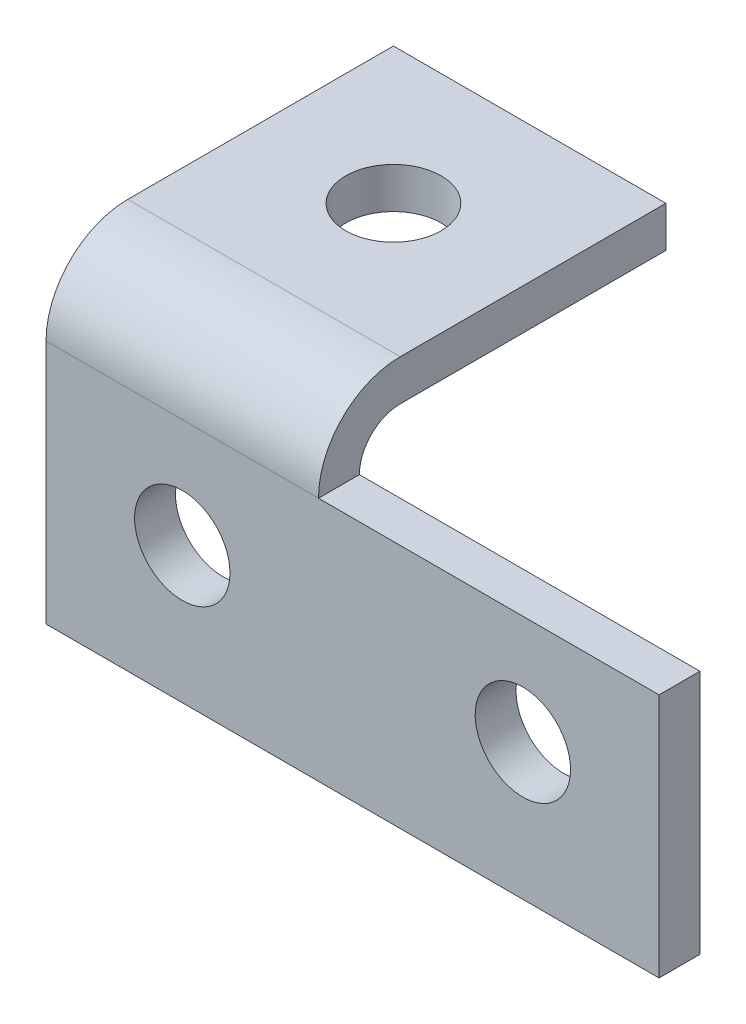
SolidWorks part; units mm, degrees
ref_plane "Front Plane" through (0, 0, 0) normal (0, 0, 1) x (1, 0, 0)
ref_plane "Top Plane" through (0, 0, 0) normal (0, 1, 0) x (1, 0, 0)
ref_plane "Right Plane" through (0, 0, 0) normal (1, 0, 0) x (0, 0, -1)
ref_plane "Plane1" through (-50, 0, 0) normal (1, 0, 0) x (0, 0, -1)
sketch "Sketch1" plane through (-50, 0, 0) normal (1, 0, 0) x (0, 0, -1)
  line L0 (0, 0) -> (51, 0)
  line L1 (51, 0) -> (51, 48)
  line L2 (51, 48) -> (12, 48)
  line L3 (0, 36) -> (0, 0)
  arc A0 (12, 48) -> (0, 36) centre (12, 36) ccw
extrude "Boss-Extrude1" add sketch "Sketch1" against normal blind 40
sketch "Sketch2" plane through (-90, 0, 0) normal (-1, 0, 0) x (0, 0, 1)
  line L0 (-51, 0) -> (-6, 0)
  line L1 (-6, 0) -> (-6, 36)
  line L2 (-12, 42) -> (-51, 42)
  line L3 (-51, 42) -> (-51, 0)
  arc A0 (-6, 36) -> (-12, 42) centre (-12, 36) ccw
extrude "Cut-Extrude1" cut sketch "Sketch2" against normal through all
sketch "Sketch3" plane through (-50, 0, 0) normal (1, 0, 0) x (0, 0, -1)
  line L0 (6, 0) -> (0, 0)
  line L1 (0, 0) -> (0, 36)
  line L2 (0, 36) -> (6, 36)
  line L3 (6, 36) -> (6, 0)
extrude "Boss-Extrude2" add sketch "Sketch3" along normal blind 50
hole_wizard "Ø14.0 (14) Diameter Hole1" positions "Sketch5" profile "Sketch4" hole size "Ø14.0" standard "ANSI Metric"
sketch "Sketch5" plane through (0, 0, 0) normal (0, 0, 1) x (1, 0, 0)
  point P0 (-70, 20)
sketch "Sketch4" plane through (-70, 20, 0) normal (1, 0, 0) x (0, -1, 0)
  line L0 (0, 0) -> (0, 51)
  line L1 (0, 51) -> (7, 51)
  line L2 (7, 51) -> (7, 0)
  line L5 (7, 0) -> (0, 0)
  line L11 (0, -6.35) -> (0, 107.95) construction
  dimension "Thru Hole Dia." = 14
  dimension "Thru Hole Depth" = 51
hole_wizard "Ø14.0 (14) Diameter Hole2" positions "Sketch7" profile "Sketch6" hole size "Ø14.0" standard "ANSI Metric"
sketch "Sketch7" plane through (0, 0, -6) normal (0, 0, -1) x (-1, 0, 0)
  point P0 (20, 20)
sketch "Sketch6" plane through (-20, 20, -6) normal (1, 0, 0) x (0, 1, 0)
  line L0 (0, 0) -> (0, 6)
  line L1 (0, 6) -> (7, 6)
  line L2 (7, 6) -> (7, 0)
  line L5 (7, 0) -> (0, 0)
  line L11 (0, -6.35) -> (0, 107.95) construction
  dimension "Thru Hole Dia." = 14
  dimension "Thru Hole Depth" = 6
hole_wizard "Ø14.0 (14) Diameter Hole3" positions "Sketch9" profile "Sketch8" hole size "Ø14.0" standard "ANSI Metric"
sketch "Sketch9" plane through (0, 42, 0) normal (0, -1, 0) x (-1, 0, 0)
  point P0 (70, 31)
sketch "Sketch8" plane through (-70, 42, -31) normal (1, 0, 0) x (0, 0, -1)
  line L0 (0, 0) -> (0, 6)
  line L1 (0, 6) -> (7, 6)
  line L2 (7, 6) -> (7, 0)
  line L5 (7, 0) -> (0, 0)
  line L11 (0, -6.35) -> (0, 107.95) construction
  dimension "Thru Hole Dia." = 14
  dimension "Thru Hole Depth" = 6
